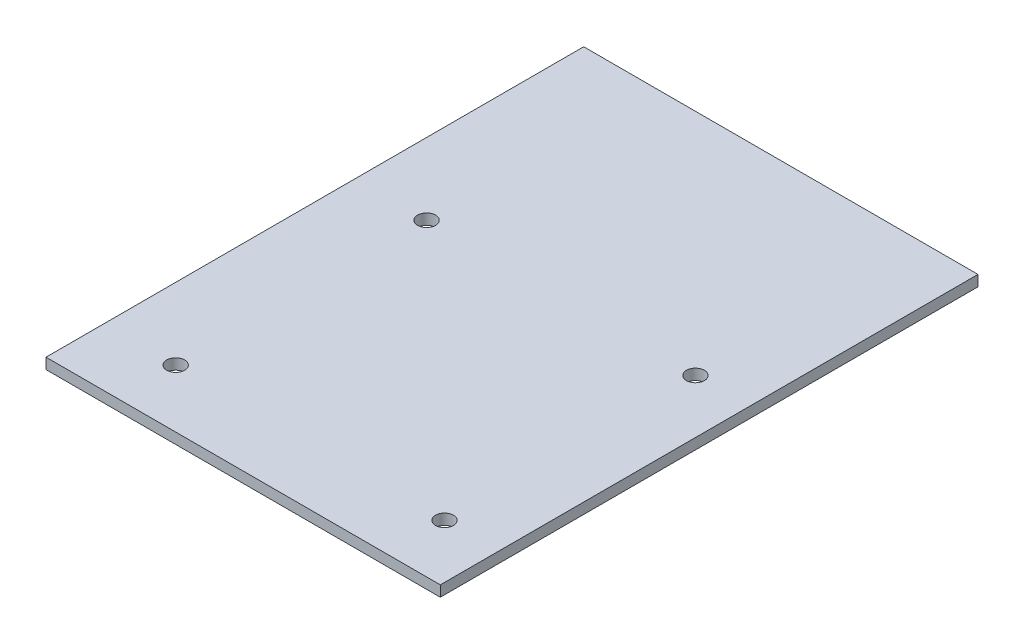
SolidWorks part; units mm, degrees
ref_plane "Front Plane" through (0, 0, 0) normal (0, 0, 1) x (1, 0, 0)
ref_plane "Top Plane" through (0, 0, 0) normal (0, 1, 0) x (1, 0, 0)
ref_plane "Right Plane" through (0, 0, 0) normal (1, 0, 0) x (0, 0, -1)
sketch "Sketch1" plane through (0, 0, 0) normal (0, 1, 0) x (1, 0, 0)
  line L1 (-110, 150) -> (110, 150)
  line L2 (-110, 150) -> (-110, -150)
  line L3 (-110, -150) -> (110, -150)
  line L4 (110, 150) -> (110, -150)
  dimension "D1" = 220
  dimension "D2" = 300
  dimension "D3" = 110
  dimension "D4" = 150
extrude "Boss-Extrude1" add sketch "Sketch1" along normal blind 6
hole_wizard "Ø10.0 (10) Diameter Hole1" positions "Sketch4" profile "Sketch3" hole size "Ø10.0" standard "ISO"
sketch "Sketch4" plane through (0, 0, 0) normal (0, -1, 0) x (1, 0, 0)
  line L0 (-110, -150) -> (-110, 150) construction
  point P0 (-70, 117.651)
  point P1 (80, 117.651)
  point P3 (80, -22.349)
  point P5 (-70, -22.349)
  dimension "D1" = 150
  dimension "D2" = 140
  dimension "D3" = 150
  dimension "D4" = 40
sketch "Sketch3" plane through (-70, 0, 117.651) normal (1, 0, 0) x (0, 0, -1)
  line L0 (0, 0) -> (0, 14.0043)
  line L1 (0, 14.0043) -> (5, 11)
  line L2 (5, 11) -> (5, 0)
  line L5 (5, 0) -> (0, 0)
  line L10 (0, 14.0043) -> (-5, 11) construction
  line L11 (0, -6.35) -> (0, 107.95) construction
  dimension "Hole Dia." = 10
  dimension "Hole Depth" = 11
  dimension "Drill Angle" = 118
sketch "Sketch6" plane through (0, 0, 0) normal (0, -1, 0) x (1, 0, 0)
  line L0 (-215.1631, 53.251) -> (190.775, 53.251) construction
  circle A0 centre (-70, 117.651) radius 5 construction
  dimension "D1" = 64.4
